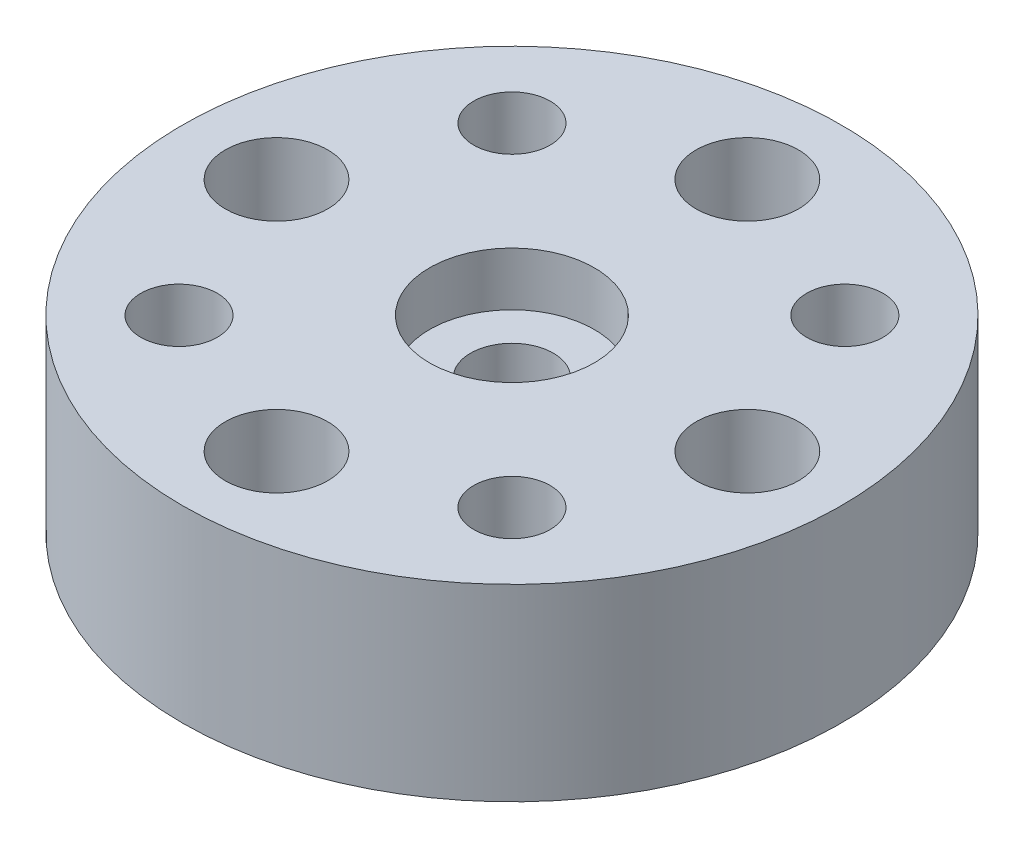
SolidWorks part; units mm, degrees
ref_plane "Front Plane" through (0, 0, 0) normal (0, 0, 1) x (1, 0, 0)
ref_plane "Top Plane" through (0, 0, 0) normal (0, 1, 0) x (1, 0, 0)
ref_plane "Right Plane" through (0, 0, 0) normal (1, 0, 0) x (0, 0, -1)
sketch "Sketch1" plane through (0, 0, 0) normal (0, 1, 0) x (1, 0, 0)
  circle A0 centre (0, 0) radius 11.1125
  dimension "D1" = 22.225
extrude "Extrude1" add sketch "Sketch1" against normal blind 6.35
sketch "Esquisse1" plane through (0, 0, 0) normal (0, 1, 0) x (1, 0, 0)
  point P0 (0, 7.9375)
  point P1 (0, -7.9375)
  point P2 (-7.9375, 0)
  point P3 (7.9375, 0)
  dimension "D1" = 15.875
  dimension "D2" = 15.875
  dimension "D3" = 7.9375
  dimension "D4" = 7.9375
hole_wizard "Dégagement #51" positions "Esquisse3" profile "Esquisse2" hole size "#5" standard "Ansi Pouces" end condition through all
sketch "Esquisse3" plane through (0, 0, 0) normal (0, 1, 0) x (-1, 0, 0)
  point P1 (7.9375, 0)
  point P4 (0, -7.9375)
  point P7 (-7.9375, 0)
  point P10 (0, 7.9375)
sketch "Esquisse2" plane through (-7.9375, 0, 0) normal (1, 0, 0) x (0, 0, 1)
  line L0 (0, 0) -> (0, 6.35)
  line L1 (0, 6.35) -> (1.7272, 6.35)
  line L2 (1.7272, 6.35) -> (1.7272, 0)
  line L5 (1.7272, 0) -> (0, 0)
  line L11 (0, -6.35) -> (0, 107.95) construction
  dimension "Diamètre du perçage jusqu'au prochain" = 3.4544
  dimension "Profondeur du perçage jusqu'au prochain" = 6.35
sketch "Esquisse5" plane through (0, -6.35, 0) normal (0, -1, 0) x (1, 0, 0)
  line L0 (0, -7.9375) -> (7.9375, 0) construction
  line L1 (0, 0) -> (3.9688, -3.9688) construction
  line L2 (-7.9375, 0) -> (0, 7.9375) construction
  line L3 (0, 7.9375) -> (7.9375, 0) construction
  line L4 (-7.9375, 0) -> (0, -7.9375) construction
  line L5 (0, -7.9375) -> (2.5624, -7.9375) construction
  line L6 (0, 0) -> (-3.9688, 3.9688) construction
  line L7 (-3.9688, -3.9688) -> (3.9688, 3.9688) construction
  point P15 (-5.6127, 5.6127)
  point P16 (5.6127, 5.6127)
  point P17 (-5.6127, -5.6127)
  point P18 (5.6127, -5.6127)
  dimension "D1" = 7.9375
  dimension "D2" = 7.9375
  dimension "D3" = 7.9375
  dimension "D4" = 7.9375
hole_wizard "Trou pour taraudage pour trou taraudé #5-401" positions "Esquisse7" profile "Esquisse6" hole size "#5-40" standard "Ansi Pouces" end condition through all
sketch "Esquisse7" plane through (0, -6.35, 0) normal (0, -1, 0) x (1, 0, 0)
  point P1 (-5.6127, -5.6127)
  point P4 (5.6127, -5.6127)
  point P7 (5.6127, 5.6127)
  point P10 (-5.6127, 5.6127)
sketch "Esquisse6" plane through (-5.6127, -6.35, -5.6127) normal (1, 0, 0) x (0, 0, -1)
  line L0 (0, 0) -> (0, 6.35)
  line L1 (0, 6.35) -> (1.289, 6.35)
  line L2 (1.289, 6.35) -> (1.289, 0)
  line L5 (1.289, 0) -> (0, 0)
  line L11 (0, -6.35) -> (0, 107.95) construction
  dimension "Diamètre du perçage jusqu'au prochain" = 2.5781
  dimension "Profondeur du perçage jusqu'au prochain" = 6.35
hole_wizard "Chambrage pour vis à tête ronde bombée #31" positions "Esquisse9" profile "Esquisse8" counterbore size "#3" standard "Ansi Pouces" end condition through all
sketch "Esquisse9" plane through (0, 0, 0) normal (0, 1, 0) x (-1, 0, 0)
  point P1 (0, 0)
sketch "Esquisse8" plane through (0, 0, 0) normal (1, 0, 0) x (0, 0, 1)
  line L0 (0, 0) -> (0, 6.35)
  line L1 (0, 6.35) -> (1.397, 6.35)
  line L3 (1.397, 6.35) -> (1.397, 1.8034)
  line L4 (1.397, 1.8034) -> (2.7788, 1.8034)
  line L5 (2.7788, 1.8034) -> (2.7788, 0)
  line L7 (2.7788, 0) -> (0, 0)
  line L11 (0, -6.35) -> (0, 107.95) construction
  dimension "Diamètre du perçage jusqu'au prochain" = 2.794
  dimension "Profondeur du perçage jusqu'au prochain" = 6.35
  dimension "Diamètre du chambrage" = 5.5575
  dimension "Profondeur du chambrage" = 1.8034
sketch "Esquisse10" plane through (0, -6.35, 0) normal (0, -1, 0) x (1, 0, 0)
  line L0 (0, -11.1125) -> (0, 9.6647) construction
  circle A0 centre (0, 0) radius 11.1125 construction
  circle A1 centre (0, 7.9375) radius 1.7272 construction
